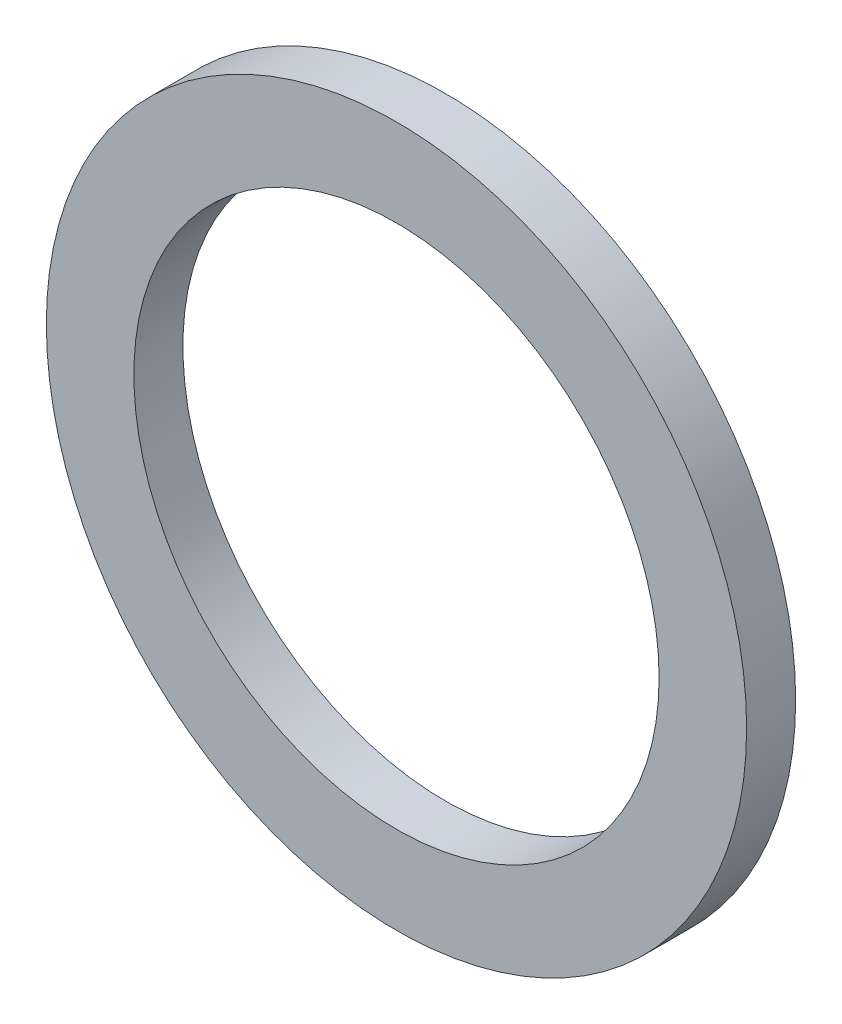
SolidWorks part; units mm, degrees
ref_plane "Front Plane" through (0, 0, 0) normal (0, 0, 1) x (1, 0, 0)
ref_plane "Top Plane" through (0, 0, 0) normal (0, 1, 0) x (1, 0, 0)
ref_plane "Right Plane" through (0, 0, 0) normal (1, 0, 0) x (0, 0, -1)
sketch "Sketch1" plane through (0, 0, 0) normal (0, 0, 1) x (1, 0, 0)
  circle A0 centre (0, 0) radius 12.7
  circle A1 centre (0, 0) radius 9.525
  dimension "D1" = 19.05
  dimension "D2" = 25.4
extrude "Boss-Extrude1" add sketch "Sketch1" along normal blind 1.778
